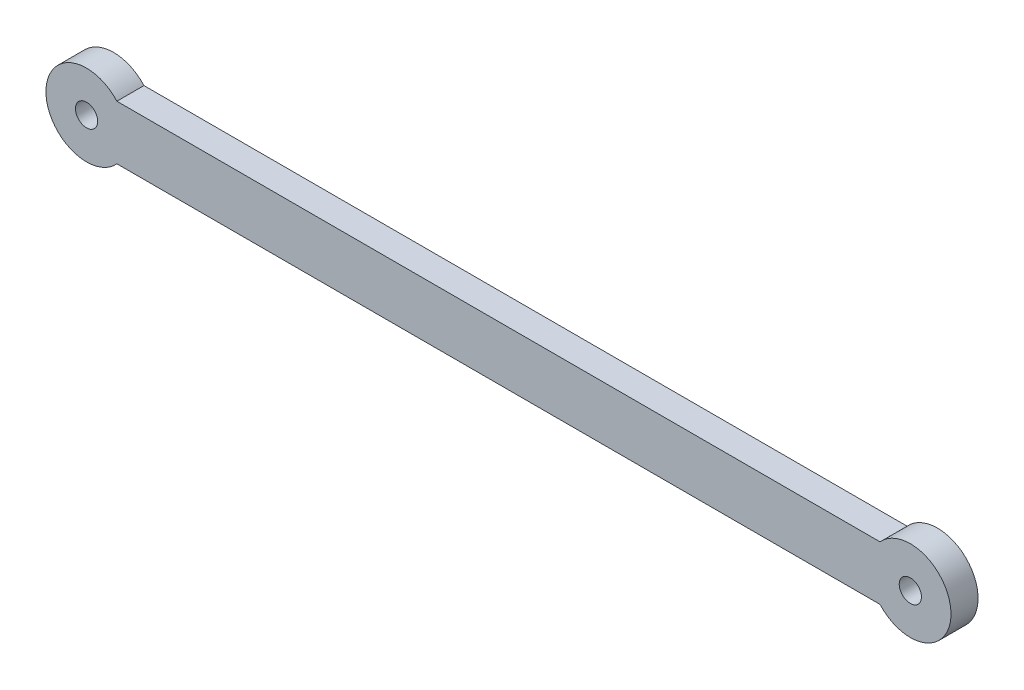
SolidWorks part; units mm, degrees
material "Acrílico (Impacto medio-alto)"
ref_plane "Piano frontale" through (0, 0, 0) normal (0, 0, 1) x (1, 0, 0)
ref_plane "Piano superiore" through (0, 0, 0) normal (0, 1, 0) x (1, 0, 0)
ref_plane "Piano destro" through (0, 0, 0) normal (1, 0, 0) x (0, 0, -1)
sketch "Schizzo1" plane through (0, 0, 0) normal (0, 0, 1) x (1, 0, 0)
  line L0 (0, 0) -> (2.05, 0) construction
  line L1 (5.5902, -5) -> (146.4098, -5)
  line L2 (5.5902, 5) -> (146.4098, 5)
  line L3 (0, 5) -> (152, 5) construction
  line L4 (0, -5) -> (152, -5) construction
  line L5 (149.95, 0) -> (152, 0) construction
  line L6 (0, 0) -> (152, 0) construction
  circle A0 centre (0, 0) radius 2.05
  circle A1 centre (152, 0) radius 2.05
  arc A2 (5.5902, 5) -> (5.5902, -5) centre (0, 0) ccw
  arc A3 (146.4098, -5) -> (146.4098, 5) centre (152, 0) ccw
  point P13 (0, 0)
  dimension "D1" = 4.1
  dimension "D4" = 15
  dimension "D5" = 15
  dimension "D3" = 152
  dimension "D6" = 5
  dimension "D7" = 5
extrude "Estrusione-Estrusione1" add sketch "Schizzo1" along normal blind 5
